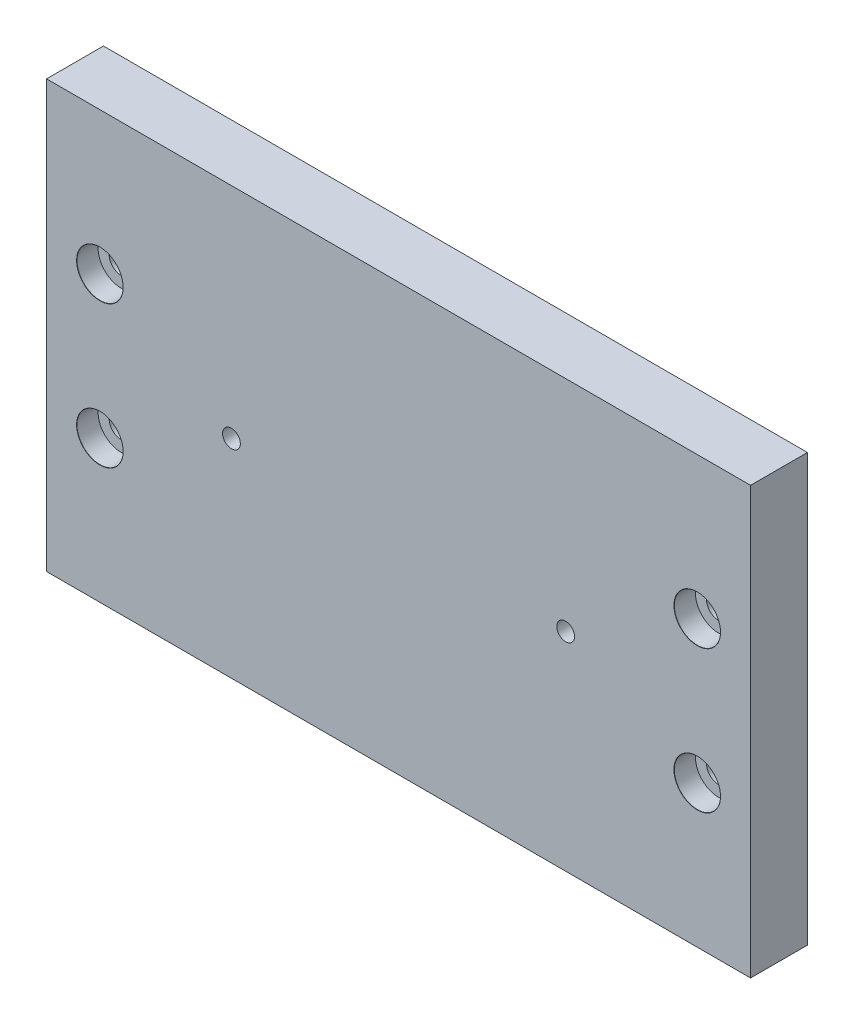
SolidWorks part; units mm, degrees
ref_plane "Front Plane" through (0, 0, 0) normal (0, 0, 1) x (1, 0, 0)
ref_plane "Top Plane" through (0, 0, 0) normal (0, 1, 0) x (1, 0, 0)
ref_plane "Right Plane" through (0, 0, 0) normal (1, 0, 0) x (0, 0, -1)
sketch "Sketch1" plane through (0, 0, 0) normal (0, 0, 1) x (1, 0, 0)
  line L1 (-49.5, -30) -> (49.5, -30)
  line L2 (-49.5, -30) -> (-49.5, 30)
  line L3 (-49.5, 30) -> (49.5, 30)
  line L4 (49.5, -30) -> (49.5, 30)
  line L5 (-49.5, -30) -> (49.5, 30) construction
  line L6 (-49.5, 30) -> (49.5, -30) construction
  point P0 (0, 0)
  dimension "D1" = 99
  dimension "D2" = 60
extrude "Boss-Extrude1" add sketch "Sketch1" along normal mid plane 8
hole_wizard "CBORE for M3 SHCS1" positions "Sketch2" profile "Sketch3" counterbore size "M3" standard "ANSI Metric" end condition through all
sketch "Sketch2" plane through (0, 0, 4) normal (0, 0, 1) x (1, 0, 0)
  line L0 (-49.5, 30) -> (-49.5, -30) construction
  line L1 (49.5, 30) -> (-49.5, 30) construction
  point P0 (-42, 10)
  point P2 (-42, -10)
  point P7 (0, 0)
  dimension "D1" = 7.5
  dimension "D2" = 20
  dimension "D3" = 20
sketch "Sketch3" plane through (-42, 10, 4) normal (1, 0, 0) x (0, -1, 0)
  line L0 (0, 0) -> (0, 8)
  line L1 (1.7, 7.975) -> (1.725, 8)
  line L2 (3.25, 3) -> (1.7, 3)
  line L3 (1.7, 3) -> (1.7, 7.975)
  line L5 (3.25, 3) -> (3.25, 0.025)
  line L6 (3.25, 0.025) -> (3.275, 0)
  line L7 (3.275, 0) -> (0, 0)
  line L8 (-3.25, 0.025) -> (-3.275, 0) construction
  line L11 (0, -6.35) -> (0, 107.95) construction
  line L12 (1.725, 8) -> (0, 8)
  line L13 (-1.7, 7.975) -> (-1.725, 8) construction
  dimension "Thru Hole Dia." = 3.4
  dimension "Thru Hole Depth" = 8
  dimension "C'Bore Dia." = 6.5
  dimension "C'Bore Depth" = 3
  dimension "Near C'Sink Dia." = 6.55
  dimension "Near C'Sink Angle" = 90
  dimension "Far C'Sink Dia." = 3.45
  dimension "Far C'Sink Angle" = 90
hole_wizard "M3x0.5 Tapped Hole1" positions "Sketch6" profile "Sketch8" tap size "M3x0.5" standard "ANSI Metric" end condition through all
sketch "Sketch6" plane through (0, 0, 4) normal (0, 0, 1) x (1, 0, 0)
  line L0 (-49.5, 30) -> (-49.5, -30) construction
  line L3 (49.5, 30) -> (-49.5, 30) construction
  point P0 (-23.5, -0.8)
  point P9 (-23.5, 0)
  point P10 (0, 0)
  point P13 (0, 0)
  point P17 (0, 0)
  dimension "D1" = 26
  dimension "D2" = 30.8
sketch "Sketch8" plane through (-23.5, -0.8, 4) normal (1, 0, 0) x (0, -1, 0)
  line L0 (0, 0) -> (0, 8)
  line L1 (0, 8) -> (1.25, 8)
  line L2 (1.25, 8) -> (1.25, 0)
  line L5 (1.25, 0) -> (0, 0)
  line L11 (0, -6.35) -> (0, 107.95) construction
  dimension "Thru Tap Drill Dia." = 2.5
  dimension "Thru Tap Drill Depth" = 8
cosmetic thread "Hole Thread1"
mirror "Mirror1" about plane through (0, 0, 0) normal (1, 0, 0) of "M3x0.5 Tapped Hole1", "CBORE for M3 SHCS1"
cosmetic thread "Hole Thread2"
